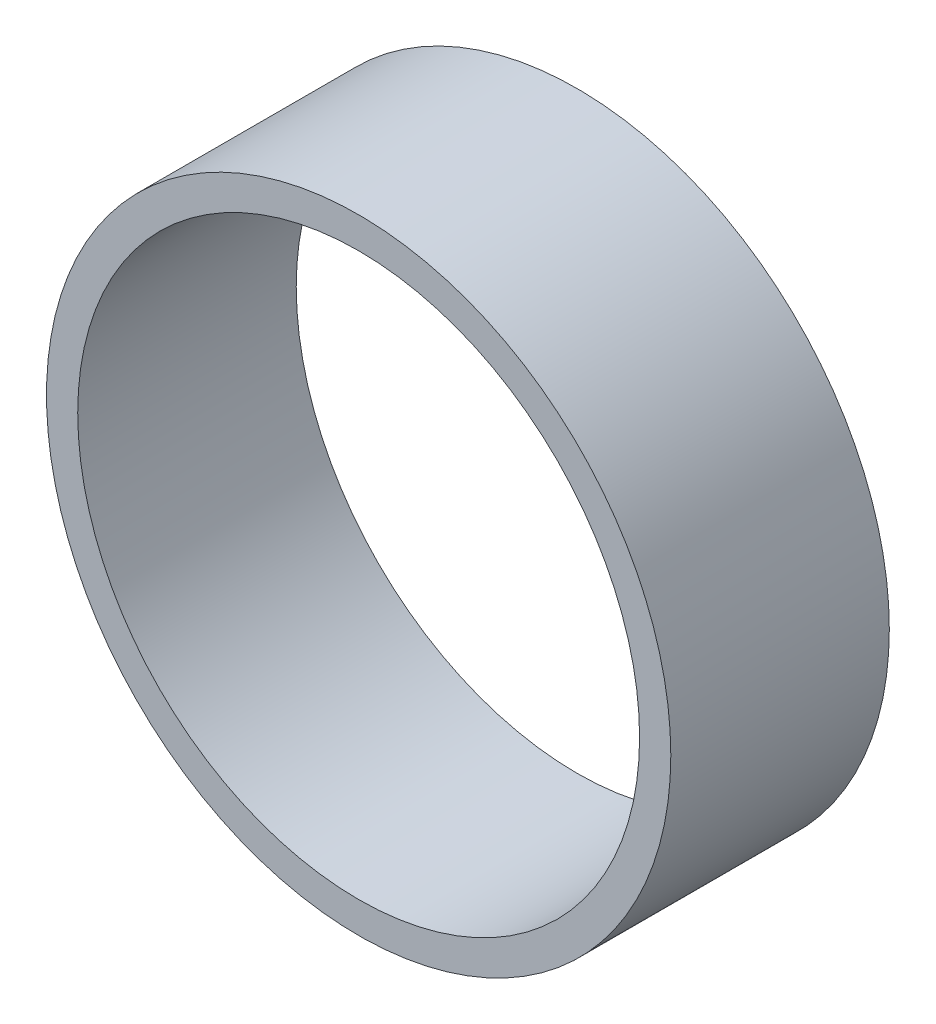
SolidWorks part; units mm, degrees
ref_plane "前视基准面" through (0, 0, 0) normal (0, 0, 1) x (1, 0, 0)
ref_plane "上视基准面" through (0, 0, 0) normal (0, 1, 0) x (1, 0, 0)
ref_plane "右视基准面" through (0, 0, 0) normal (1, 0, 0) x (0, 0, -1)
sketch "草图2" plane through (0, 0, 0) normal (0, 0, 1) x (1, 0, 0)
  circle A0 centre (0, 0) radius 10
  dimension "D1" = 20
extrude "拉伸-薄壁1" add sketch "草图2" along normal blind 7 thin contours A0 thin type one direction reverse wall 1
